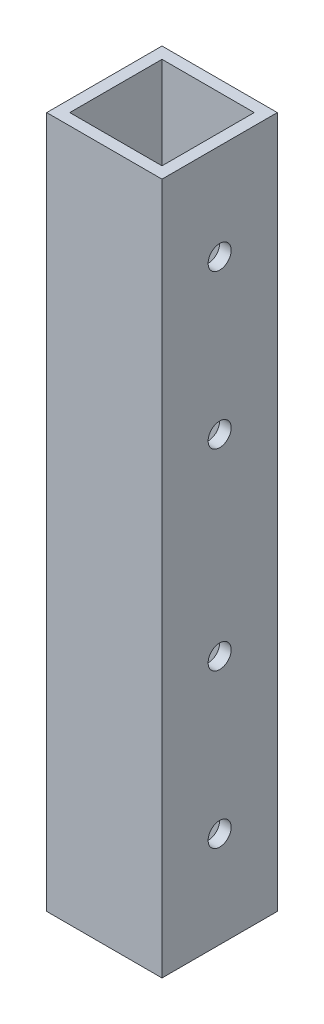
SolidWorks part; units mm, degrees
material "6061 Alloy"
ref_plane "Front Plane" through (0, 0, 0) normal (0, 0, 1) x (1, 0, 0)
ref_plane "Top Plane" through (0, 0, 0) normal (0, 1, 0) x (1, 0, 0)
ref_plane "Right Plane" through (0, 0, 0) normal (1, 0, 0) x (0, 0, -1)
sketch "Sketch1" plane through (0, 0, 0) normal (0, 1, 0) x (1, 0, 0)
  line L1 (0, 0) -> (15, 0)
  line L2 (0, 0) -> (0, 15)
  line L3 (0, 15) -> (15, 15)
  line L4 (15, 0) -> (15, 15)
  dimension "D1" = 15
extrude "Extrude-Thin1" add sketch "Sketch1" along normal blind 90 thin thin type one direction reverse wall 1.5
sketch "Sketch2" plane through (15, 0, 0) normal (1, 0, 0) x (0, 0, -1)
  line L0 (0, 0) -> (15, 0) construction
  line L1 (15, 90) -> (15, 0) construction
  circle A0 centre (7.5, 12.5) radius 1.5
  circle A1 centre (7.5, 32.5) radius 1.5
  circle A2 centre (7.5, 57.5) radius 1.5
  circle A3 centre (7.5, 77.5) radius 1.5
  dimension "D1" = 3
  dimension "D2" = 7.5
  dimension "D3" = 12.5
  dimension "D4" = 32.5
  dimension "D5" = 57.5
  dimension "D6" = 77.5
extrude "Cut-Extrude1" cut sketch "Sketch2" against normal through all
